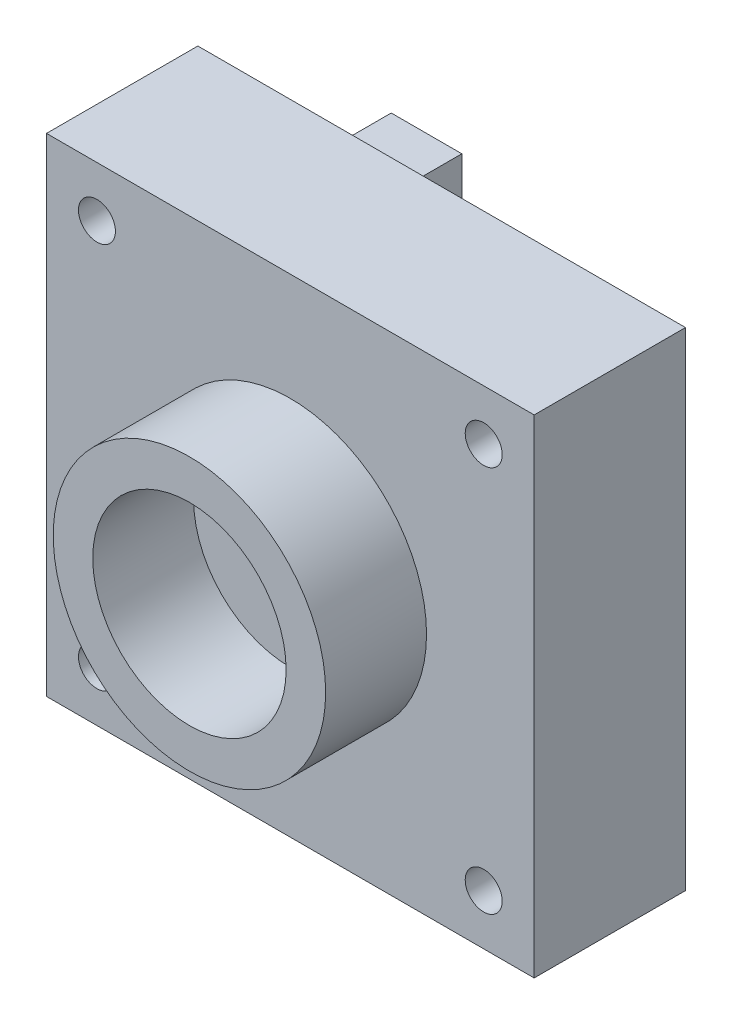
SolidWorks part; units mm, degrees
ref_plane "Front Plane" through (0, 0, 0) normal (0, 0, 1) x (1, 0, 0)
ref_plane "Top Plane" through (0, 0, 0) normal (0, 1, 0) x (1, 0, 0)
ref_plane "Right Plane" through (0, 0, 0) normal (1, 0, 0) x (0, 0, -1)
sketch "Sketch1" plane through (0, 0, 0) normal (0, 0, 1) x (1, 0, 0)
  line L1 (0, 0) -> (29, 0)
  line L2 (0, 0) -> (0, 29)
  line L3 (0, 29) -> (29, 29)
  line L4 (29, 0) -> (29, 29)
  dimension "D1" = 29
  dimension "D2" = 29
extrude "Boss-Extrude1" add sketch "Sketch1" along normal blind 9
sketch "Sketch3" plane through (0, 0, 9) normal (0, 0, 1) x (1, 0, 0)
  line L0 (0, 29) -> (29, 0) construction
  circle A0 centre (14.5, 14.5) radius 8.1
  dimension "D1" = 16.2
extrude "Boss-Extrude2" add sketch "Sketch3" along normal blind 6 contours A0
sketch "Sketch4" plane through (0, 0, 15) normal (0, 0, 1) x (1, 0, 0)
  circle A0 centre (14.5, 14.5) radius 5.75
  circle A1 centre (14.5, 14.5) radius 8.1 construction
  dimension "D1" = 11.5
extrude "Cut-Extrude1" cut sketch "Sketch4" against normal blind 6
sketch "Sketch5" plane through (0, 0, 0) normal (0, 0, -1) x (-1, 0, 0)
  line L0 (-14.5, 29) -> (-14.5, 0) construction
  line L2 (-29, 29) -> (0, 29) construction
  line L3 (0, 0) -> (-29, 0) construction
  line L4 (-14.5, 14.5) -> (0, 14.5) construction
  line L5 (0, 29) -> (0, 0) construction
  circle A0 centre (-26, 26) radius 1.1
  circle A1 centre (-3, 26) radius 1.1
  circle A4 centre (-3, 3) radius 1.1
  circle A5 centre (-26, 3) radius 1.1
  dimension "D1" = 2.2
  dimension "D5" = 2.2
  dimension "D2" = 11.5
  dimension "D3" = 11.5
  dimension "D4" = 11.5
extrude "Cut-Extrude2" cut sketch "Sketch5" against normal through all
sketch "Sketch6" plane through (0, 0, 0) normal (0, 0, -1) x (-1, 0, 0)
  line L0 (-28, 28) -> (-28, 1)
  line L1 (-28, 1) -> (-1, 1)
  line L2 (-1, 1) -> (-1, 8)
  line L3 (-1, 8) -> (-7.5, 8)
  line L4 (-7.5, 8) -> (-7.5, 21)
  line L5 (-7.5, 21) -> (-1, 21)
  line L6 (-1, 21) -> (-1, 28)
  line L7 (-1, 28) -> (-28, 28)
  line L8 (-29, 14.5) -> (0, 14.5) construction
  line L9 (-29, 0) -> (-29, 29) construction
  line L10 (0, 29) -> (0, 0) construction
  line L11 (-29, 29) -> (0, 29) construction
  line L12 (0, 0) -> (-29, 0) construction
  circle A0 centre (-26, 3) radius 1.1 construction
  circle A1 centre (-3, 3) radius 1.1 construction
  circle A2 centre (-3, 26) radius 1.1 construction
  circle A3 centre (-26, 26) radius 1.1 construction
  circle A4 centre (-26, 3) radius 1.1
  circle A5 centre (-3, 3) radius 1.1
  circle A6 centre (-3, 26) radius 1.1
  circle A7 centre (-26, 26) radius 1.1
  point P14 (-7.5, 14.5)
  dimension "D1" = 13
  dimension "D2" = 6.5
  dimension "D3" = 1
  dimension "D4" = 1
  dimension "D5" = 1
  dimension "D6" = 1
extrude "Boss-Extrude3" add sketch "Sketch6" along normal blind 0.5
sketch "Sketch7" plane through (0, 0, 0) normal (0, 0, -1) x (-1, 0, 0)
  line L0 (-14.5, 29) -> (-14.5, 0) construction
  line L1 (-29, 29) -> (0, 29) construction
  line L2 (0, 0) -> (-29, 0) construction
  line L3 (-14.5, 14.5) -> (-29, 14.5) construction
  line L4 (-29, 0) -> (-29, 29) construction
  circle A0 centre (-26, 26) radius 2
  circle A1 centre (-3, 26) radius 2
  circle A2 centre (-3, 3) radius 2
  circle A3 centre (-26, 3) radius 2
  circle A4 centre (-3, 26) radius 1.1 construction
  circle A5 centre (-3, 3) radius 1.1 construction
  circle A6 centre (-26, 3) radius 1.1 construction
  circle A7 centre (-26, 26) radius 1.1 construction
  circle A8 centre (-3, 26) radius 1.1
  circle A9 centre (-3, 3) radius 1.1
  circle A10 centre (-26, 3) radius 1.1
  circle A11 centre (-26, 26) radius 1.1
  dimension "D1" = 4
extrude "Boss-Extrude4" add sketch "Sketch7" along normal blind 1
sketch "Sketch8" plane through (0, 0, 0) normal (0, 0, -1) x (-1, 0, 0)
  line L0 (0, 29) -> (0, 0) construction
  line L1 (-7.5, 21) -> (0, 21)
  line L2 (-7.5, 21) -> (-7.5, 8)
  line L3 (-7.5, 8) -> (0, 8)
  line L4 (0, 21) -> (0, 8)
  line L5 (-1, 8) -> (-7.5, 8) construction
extrude "Boss-Extrude5" add sketch "Sketch8" along normal blind 3 separate body
fillet "Fillet1" radius 1 3 edges at (7.5, 14.5, -3) (3.75, 21, -3) (3.75, 8, -3)
sketch "Sketch9" plane through (0, 0, 0) normal (-1, 0, 0) x (0, 0, 1)
  line L0 (-2, 21) -> (0, 21) construction
  line L1 (-2.25, 20.25) -> (-0.75, 20.25)
  line L2 (-2.25, 20.25) -> (-2.25, 16.25)
  line L3 (-2.25, 16.25) -> (-0.75, 16.25)
  line L4 (-0.75, 20.25) -> (-0.75, 16.25)
  line L5 (-2.25, 15.25) -> (-0.75, 15.25)
  line L6 (-2.25, 15.25) -> (-2.25, 8.75)
  line L7 (-2.25, 8.75) -> (-0.75, 8.75)
  line L8 (-0.75, 15.25) -> (-0.75, 8.75)
  line L9 (-2, 8) -> (0, 8) construction
  line L10 (0, 29) -> (0, 0) construction
  line L11 (-3, 9) -> (-3, 20) construction
  dimension "D1" = 1
  dimension "D2" = 0.75
  dimension "D3" = 0.75
  dimension "D4" = 0.75
  dimension "D5" = 0.75
  dimension "D6" = 6.5
extrude "Cut-Extrude3" cut sketch "Sketch9" against normal blind 2
sketch "Sketch10" plane through (0, 0, -0.5) normal (0, 0, -1) x (-1, 0, 0)
  line L0 (0, 29) -> (0, 0) construction
  line L1 (-6.4, 26.2) -> (-10.6, 26.2)
  line L2 (-6.4, 26.2) -> (-6.4, 23.1)
  line L3 (-6.4, 23.1) -> (-10.6, 23.1)
  line L4 (-10.6, 26.2) -> (-10.6, 23.1)
  line L5 (-29, 29) -> (0, 29) construction
  dimension "D1" = 4.2
  dimension "D2" = 3.1
  dimension "D3" = 6.4
  dimension "D4" = 2.8
extrude "Boss-Extrude6" add sketch "Sketch10" along normal blind 4.6
sketch "Sketch11" plane through (0, 0, -0.5) normal (0, 0, -1) x (-1, 0, 0)
  line L0 (-29, 0) -> (-29, 29) construction
  line L1 (-23, 26) -> (-14, 26)
  line L2 (-23, 26) -> (-23, 17)
  line L3 (-23, 17) -> (-14, 17)
  line L4 (-14, 26) -> (-14, 17)
  line L5 (-27, 6) -> (-18, 6)
  line L6 (-27, 6) -> (-27, 15)
  line L7 (-27, 15) -> (-18, 15)
  line L8 (-18, 6) -> (-18, 15)
  line L9 (-27, 18.5) -> (-24.5, 18.5)
  line L10 (-27, 18.5) -> (-27, 17)
  line L11 (-27, 17) -> (-24.5, 17)
  line L12 (-24.5, 18.5) -> (-24.5, 17)
  line L13 (-26.75, 22.5) -> (-24.75, 22.5)
  line L14 (-26.75, 22.5) -> (-26.75, 19.5)
  line L15 (-26.75, 19.5) -> (-24.75, 19.5)
  line L16 (-24.75, 22.5) -> (-24.75, 19.5)
  line L17 (0, 0) -> (-29, 0) construction
  line L18 (-29, 29) -> (0, 29) construction
  dimension "D1" = 9
  dimension "D2" = 9
  dimension "D3" = 9
  dimension "D4" = 9
  dimension "D5" = 2
  dimension "D6" = 6
  dimension "D7" = 3
  dimension "D8" = 6
  dimension "D9" = 1.5
  dimension "D10" = 2.5
  dimension "D11" = 2
  dimension "D12" = 3
  dimension "D13" = 2
  dimension "D14" = 1
  dimension "D15" = 0.25
extrude "Boss-Extrude7" add sketch "Sketch11" along normal blind 0.2
fillet "Fillet2" radius 0.2 4 edges at (28, 3, -1) (1, 3, -1) (5, 26, -1) (24, 26, -1)
